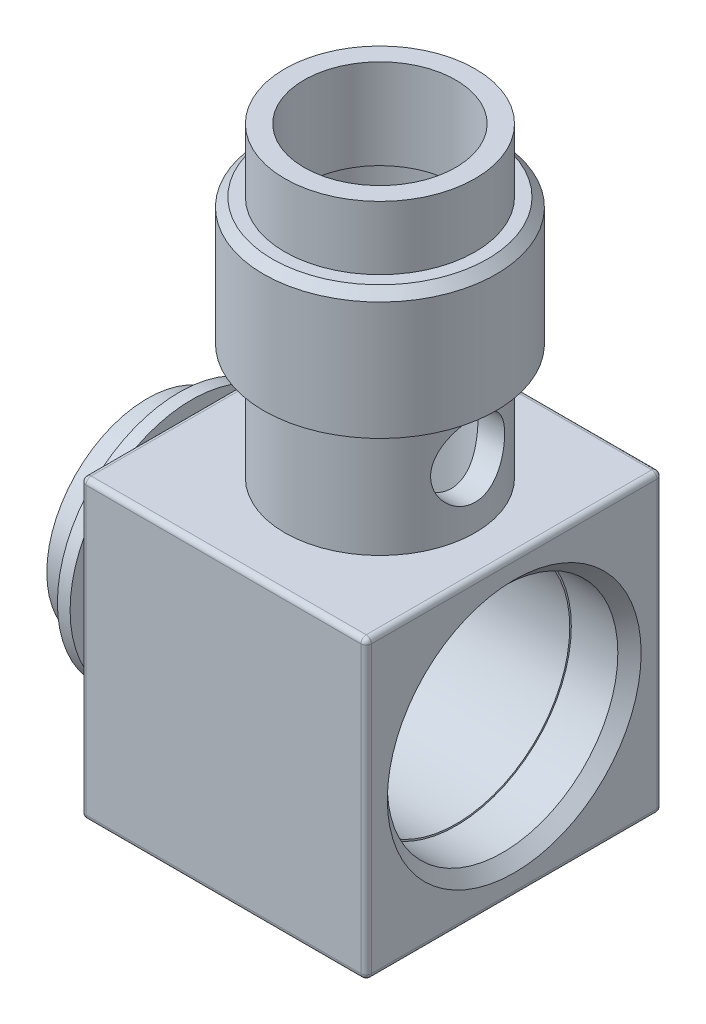
SolidWorks part; units mm, degrees
material "Сталь"
ref_plane "Спереди" through (0, 0, 0) normal (0, 0, 1) x (1, 0, 0)
ref_plane "Сверху" through (0, 0, 0) normal (0, 1, 0) x (1, 0, 0)
ref_plane "Справа" through (0, 0, 0) normal (1, 0, 0) x (0, 0, -1)
sketch "Эскиз1" plane through (0, 0, 0) normal (0, 0, 1) x (1, 0, 0)
  line L0 (0, 0) -> (53.6101, 0) construction
  line L1 (0, -7) -> (11.6, -7)
  line L2 (0, -7) -> (0, -9.5)
  line L3 (0, -9.5) -> (3, -9.5)
  line L4 (3, -9.5) -> (3, -11.5)
  line L5 (3, -11.5) -> (4.2, -11.5)
  line L6 (4.2, -11.5) -> (4.2, -9.5)
  line L7 (4.2, -9.5) -> (7.7, -9.5)
  line L8 (7.7, -9.5) -> (7.7, -14)
  line L9 (7.7, -14) -> (34.7, -14)
  line L10 (34.7, -14) -> (34.7, -10.5)
  line L11 (34.7, -10.5) -> (11.6, -10.5) construction
  line L12 (11.6, -10.5) -> (11.6, -7) construction
  line L13 (11.6, -7) -> (11.6, 0)
  line L14 (11.6, 0) -> (34.7, 0)
  line L15 (34.7, 0) -> (34.7, -10.5)
  dimension "D1" = 11.6
  dimension "D2" = 7
  dimension "D3" = 9.5
  dimension "D4" = 3
  dimension "D5" = 2
  dimension "D6" = 1.2
  dimension "D7" = 14
  dimension "D8" = 27
  dimension "D9" = 3.5
  dimension "D10" = 3.5
revolve "Повернуть1" add sketch "Эскиз1" angle 360 about L0
sketch "Эскиз2" plane through (0, 0, 0) normal (0, 1, 0) x (1, 0, 0)
  circle A0 centre (22, 0) radius 9
  dimension "D1" = 18
  dimension "D2" = 22
extrude "Бобышка-Вытянуть1" add sketch "Эскиз2" along normal blind 25
sketch "Эскиз3" plane through (0, 25, 0) normal (0, 1, 0) x (1, 0, 0)
  circle A0 centre (22, 0) radius 11
  dimension "D1" = 22
extrude "Бобышка-Вытянуть2" add sketch "Эскиз3" along normal blind 12
cosmetic thread "Условное изображение резьбы1" parameters "D2"=20.344
sketch "Эскиз4" plane through (0, 37, 0) normal (0, 1, 0) x (1, 0, 0)
  circle A0 centre (22, 0) radius 9
  dimension "D1" = 18
extrude "Бобышка-Вытянуть3" add sketch "Эскиз4" along normal blind 6
sketch "Эскиз5" plane through (34.7, 0, 0) normal (1, 0, 0) x (0, 0, -1)
  circle A0 centre (0, 0) radius 10.75
  dimension "D1" = 21.5
extrude "Вырез-Вытянуть1" cut sketch "Эскиз5" against normal up to surface (23.1 mm away) up to face at (11.6, 0, 7)
sketch "Эскиз6" plane through (0, 43, 0) normal (0, 1, 0) x (1, 0, 0)
  circle A0 centre (22, 0) radius 8.5
  dimension "D1" = 17
extrude "Вырез-Вытянуть2" cut sketch "Эскиз6" against normal blind 7 from offset 8.5 offset against normal yes
sketch "Эскиз8" plane through (0, 27.5, 0) normal (0, 1, 0) x (1, 0, 0)
  circle A0 centre (22, 0) radius 6.75
  dimension "D1" = 13.5
extrude "Вырез-Вытянуть3" cut sketch "Эскиз8" against normal up to next
sketch "Эскиз9" plane through (0, 0, 0) normal (1, 0, 0) x (0, 0, -1)
  circle A0 centre (0, 20) radius 3.5
  dimension "D2" = 7
  dimension "D1" = 20
extrude "Вырез-Вытянуть4" cut sketch "Эскиз9" along normal through all
sketch "Эскиз10" plane through (34.7, 0, 0) normal (1, 0, 0) x (0, 0, -1)
  circle A0 centre (0, 0) radius 10.75 construction
  circle A1 centre (0, 0) radius 10.75
extrude "Бобышка-Вытянуть4" add sketch "Эскиз10" against normal blind 5.95
chamfer "Фаска1" distance 0.828 angle 45 1 edges at (22, 37, 11)
sketch "Эскиз12" plane through (34.7, 0, 0) normal (1, 0, 0) x (0, 0, -1)
  line L1 (-14, -14) -> (14, -14)
  line L2 (-14, -14) -> (-14, 14)
  line L3 (-14, 14) -> (14, 14)
  line L4 (14, -14) -> (14, 14)
  line L5 (-14, -14) -> (14, 14) construction
  line L6 (-14, 14) -> (14, -14) construction
  circle A0 centre (0, 0) radius 14 construction
  circle A3 centre (0, 0) radius 13
  circle A4 centre (0, 0) radius 13
  point P0 (0, 0)
  dimension "D1" = 1
extrude "Бобышка-Вытянуть5" add sketch "Эскиз12" against normal up to surface (27 mm away) up to face at (7.7, 0, 14)
sketch "Эскиз13" plane through (0, 14, 0) normal (0, 1, 0) x (1, 0, 0)
  circle A1 centre (22, 0) radius 6.75
  circle A2 centre (22, 0) radius 6.75
  dimension "D1" = 0
extrude "Вырез-Вытянуть5" cut sketch "Эскиз13" against normal up to next
sketch "Эскиз14" plane through (0, 43, 0) normal (0, 1, 0) x (1, 0, 0)
  circle A0 centre (22, 0) radius 7.172
  dimension "D1" = 14.344
extrude "Вырез-Вытянуть6" cut sketch "Эскиз14" against normal up to next
cosmetic thread "Условное изображение резьбы2" parameters "D2"=16
sketch "Эскиз16" plane through (34.7, 0, 0) normal (1, 0, 0) x (0, 0, -1)
  circle A0 centre (0, 0) radius 10.8985
  dimension "D1" = 21.797
extrude "Вырез-Вытянуть7" cut sketch "Эскиз16" against normal blind 5.5
cosmetic thread "Условное изображение резьбы3" parameters "D1"=5.5, "D2"=24
chamfer "Фаска3" distance 1.1015 angle 45 1 edges at (34.7, 0, -10.8985)
sketch "Эскиз18" plane through (28.75, 0, 0) normal (-1, 0, 0) x (0, 0, 1)
  circle A1 centre (0, 0) radius 10.75
  circle A2 centre (0, 0) radius 10.75
  dimension "D1" = 0
extrude "Вырез-Вытянуть11" cut sketch "Эскиз18" against normal up to next
fillet "Скругление1" radius 0.5 12 edges at (34.7, 0, -14) (7.7, 0, -14) (21.2, 14, -14) (34.7, -14, 0) (7.7, -14, 0) (21.2, -14, -14) (21.2, -14, 14) (34.7, 0, 14) (7.7, 0, 14) (21.2, 14, 14) (7.7, 14, 0) (34.7, 14, 0)
